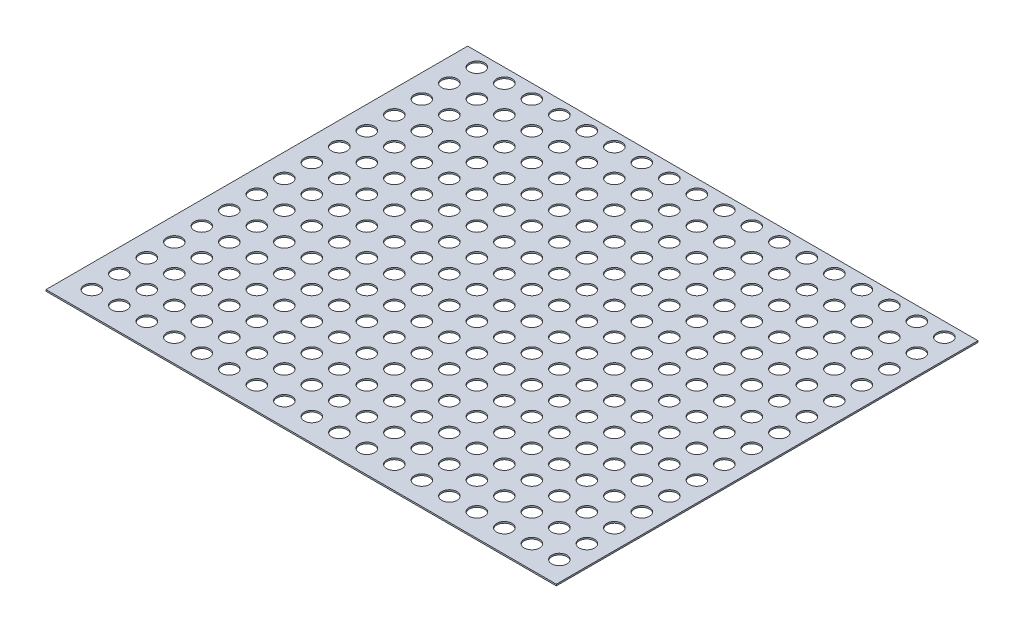
SolidWorks part; units mm, degrees
ref_plane "Спереди" through (0, 0, 0) normal (0, 0, 1) x (1, 0, 0)
ref_plane "Сверху" through (0, 0, 0) normal (0, 1, 0) x (1, 0, 0)
ref_plane "Справа" through (0, 0, 0) normal (1, 0, 0) x (0, 0, -1)
sketch "Эскиз1" plane through (0, 0, 0) normal (0, 1, 0) x (1, 0, 0)
  line L1 (167, -138) -> (-167, -138)
  line L2 (167, -138) -> (167, 138)
  line L3 (167, 138) -> (-167, 138)
  line L4 (-167, -138) -> (-167, 138)
  line L5 (167, -138) -> (-167, 138) construction
  line L6 (167, 138) -> (-167, -138) construction
  point P0 (0, 0)
  dimension "D1" = 334
  dimension "D2" = 276
extrude "Бобышка-Вытянуть1" add sketch "Эскиз1" along normal blind 1
sketch "Эскиз2" plane through (0, 1, 0) normal (0, 1, 0) x (1, 0, 0)
  line L0 (-167, 138) -> (-167, -138) construction
  line L2 (-167, -138) -> (167, -138) construction
  circle A0 centre (-152, -123) radius 5
  circle A1 centre (-134, -123) radius 5
  circle A2 centre (-116, -123) radius 5
  circle A3 centre (-98, -123) radius 5
  circle A4 centre (-80, -123) radius 5
  circle A5 centre (-62, -123) radius 5
  circle A6 centre (-44, -123) radius 5
  circle A7 centre (-26, -123) radius 5
  circle A8 centre (-8, -123) radius 5
  circle A9 centre (10, -123) radius 5
  circle A10 centre (28, -123) radius 5
  circle A11 centre (46, -123) radius 5
  circle A12 centre (64, -123) radius 5
  circle A13 centre (82, -123) radius 5
  circle A14 centre (100, -123) radius 5
  circle A15 centre (118, -123) radius 5
  circle A16 centre (136, -123) radius 5
  circle A17 centre (154, -123) radius 5
  circle A20 centre (-134, -105) radius 5
  circle A21 centre (-116, -105) radius 5
  circle A22 centre (-98, -105) radius 5
  circle A23 centre (-80, -105) radius 5
  circle A24 centre (-62, -105) radius 5
  circle A25 centre (-44, -105) radius 5
  circle A26 centre (-26, -105) radius 5
  circle A27 centre (-8, -105) radius 5
  circle A28 centre (10, -105) radius 5
  circle A29 centre (28, -105) radius 5
  circle A30 centre (46, -105) radius 5
  circle A31 centre (64, -105) radius 5
  circle A32 centre (82, -105) radius 5
  circle A33 centre (100, -105) radius 5
  circle A34 centre (118, -105) radius 5
  circle A35 centre (136, -105) radius 5
  circle A36 centre (154, -105) radius 5
  circle A39 centre (-134, -87) radius 5
  circle A40 centre (-116, -87) radius 5
  circle A41 centre (-98, -87) radius 5
  circle A42 centre (-80, -87) radius 5
  circle A43 centre (-62, -87) radius 5
  circle A44 centre (-44, -87) radius 5
  circle A45 centre (-26, -87) radius 5
  circle A46 centre (-8, -87) radius 5
  circle A47 centre (10, -87) radius 5
  circle A48 centre (28, -87) radius 5
  circle A49 centre (46, -87) radius 5
  circle A50 centre (64, -87) radius 5
  circle A51 centre (82, -87) radius 5
  circle A52 centre (100, -87) radius 5
  circle A53 centre (118, -87) radius 5
  circle A54 centre (136, -87) radius 5
  circle A55 centre (154, -87) radius 5
  circle A58 centre (-134, -69) radius 5
  circle A59 centre (-116, -69) radius 5
  circle A60 centre (-98, -69) radius 5
  circle A61 centre (-80, -69) radius 5
  circle A62 centre (-62, -69) radius 5
  circle A63 centre (-44, -69) radius 5
  circle A64 centre (-26, -69) radius 5
  circle A65 centre (-8, -69) radius 5
  circle A66 centre (10, -69) radius 5
  circle A67 centre (28, -69) radius 5
  circle A68 centre (46, -69) radius 5
  circle A69 centre (64, -69) radius 5
  circle A70 centre (82, -69) radius 5
  circle A71 centre (100, -69) radius 5
  circle A72 centre (118, -69) radius 5
  circle A73 centre (136, -69) radius 5
  circle A74 centre (154, -69) radius 5
  circle A77 centre (-134, -51) radius 5
  circle A78 centre (-116, -51) radius 5
  circle A79 centre (-98, -51) radius 5
  circle A80 centre (-80, -51) radius 5
  circle A81 centre (-62, -51) radius 5
  circle A82 centre (-44, -51) radius 5
  circle A83 centre (-26, -51) radius 5
  circle A84 centre (-8, -51) radius 5
  circle A85 centre (10, -51) radius 5
  circle A86 centre (28, -51) radius 5
  circle A87 centre (46, -51) radius 5
  circle A88 centre (64, -51) radius 5
  circle A89 centre (82, -51) radius 5
  circle A90 centre (100, -51) radius 5
  circle A91 centre (118, -51) radius 5
  circle A92 centre (136, -51) radius 5
  circle A93 centre (154, -51) radius 5
  circle A96 centre (-134, -33) radius 5
  circle A97 centre (-116, -33) radius 5
  circle A98 centre (-98, -33) radius 5
  circle A99 centre (-80, -33) radius 5
  circle A100 centre (-62, -33) radius 5
  circle A101 centre (-44, -33) radius 5
  circle A102 centre (-26, -33) radius 5
  circle A103 centre (-8, -33) radius 5
  circle A104 centre (10, -33) radius 5
  circle A105 centre (28, -33) radius 5
  circle A106 centre (46, -33) radius 5
  circle A107 centre (64, -33) radius 5
  circle A108 centre (82, -33) radius 5
  circle A109 centre (100, -33) radius 5
  circle A110 centre (118, -33) radius 5
  circle A111 centre (136, -33) radius 5
  circle A112 centre (154, -33) radius 5
  circle A115 centre (-134, -15) radius 5
  circle A116 centre (-116, -15) radius 5
  circle A117 centre (-98, -15) radius 5
  circle A118 centre (-80, -15) radius 5
  circle A119 centre (-62, -15) radius 5
  circle A120 centre (-44, -15) radius 5
  circle A121 centre (-26, -15) radius 5
  circle A122 centre (-8, -15) radius 5
  circle A123 centre (10, -15) radius 5
  circle A124 centre (28, -15) radius 5
  circle A125 centre (46, -15) radius 5
  circle A126 centre (64, -15) radius 5
  circle A127 centre (82, -15) radius 5
  circle A128 centre (100, -15) radius 5
  circle A129 centre (118, -15) radius 5
  circle A130 centre (136, -15) radius 5
  circle A131 centre (154, -15) radius 5
  circle A134 centre (-134, 3) radius 5
  circle A135 centre (-116, 3) radius 5
  circle A136 centre (-98, 3) radius 5
  circle A137 centre (-80, 3) radius 5
  circle A138 centre (-62, 3) radius 5
  circle A139 centre (-44, 3) radius 5
  circle A140 centre (-26, 3) radius 5
  circle A141 centre (-8, 3) radius 5
  circle A142 centre (10, 3) radius 5
  circle A143 centre (28, 3) radius 5
  circle A144 centre (46, 3) radius 5
  circle A145 centre (64, 3) radius 5
  circle A146 centre (82, 3) radius 5
  circle A147 centre (100, 3) radius 5
  circle A148 centre (118, 3) radius 5
  circle A149 centre (136, 3) radius 5
  circle A150 centre (154, 3) radius 5
  circle A153 centre (-134, 21) radius 5
  circle A154 centre (-116, 21) radius 5
  circle A155 centre (-98, 21) radius 5
  circle A156 centre (-80, 21) radius 5
  circle A157 centre (-62, 21) radius 5
  circle A158 centre (-44, 21) radius 5
  circle A159 centre (-26, 21) radius 5
  circle A160 centre (-8, 21) radius 5
  circle A161 centre (10, 21) radius 5
  circle A162 centre (28, 21) radius 5
  circle A163 centre (46, 21) radius 5
  circle A164 centre (64, 21) radius 5
  circle A165 centre (82, 21) radius 5
  circle A166 centre (100, 21) radius 5
  circle A167 centre (118, 21) radius 5
  circle A168 centre (136, 21) radius 5
  circle A169 centre (154, 21) radius 5
  circle A172 centre (-134, 39) radius 5
  circle A173 centre (-116, 39) radius 5
  circle A174 centre (-98, 39) radius 5
  circle A175 centre (-80, 39) radius 5
  circle A176 centre (-62, 39) radius 5
  circle A177 centre (-44, 39) radius 5
  circle A178 centre (-26, 39) radius 5
  circle A179 centre (-8, 39) radius 5
  circle A180 centre (10, 39) radius 5
  circle A181 centre (28, 39) radius 5
  circle A182 centre (46, 39) radius 5
  circle A183 centre (64, 39) radius 5
  circle A184 centre (82, 39) radius 5
  circle A185 centre (100, 39) radius 5
  circle A186 centre (118, 39) radius 5
  circle A187 centre (136, 39) radius 5
  circle A188 centre (154, 39) radius 5
  circle A191 centre (-134, 57) radius 5
  circle A192 centre (-116, 57) radius 5
  circle A193 centre (-98, 57) radius 5
  circle A194 centre (-80, 57) radius 5
  circle A195 centre (-62, 57) radius 5
  circle A196 centre (-44, 57) radius 5
  circle A197 centre (-26, 57) radius 5
  circle A198 centre (-8, 57) radius 5
  circle A199 centre (10, 57) radius 5
  circle A200 centre (28, 57) radius 5
  circle A201 centre (46, 57) radius 5
  circle A202 centre (64, 57) radius 5
  circle A203 centre (82, 57) radius 5
  circle A204 centre (100, 57) radius 5
  circle A205 centre (118, 57) radius 5
  circle A206 centre (136, 57) radius 5
  circle A207 centre (154, 57) radius 5
  circle A210 centre (-134, 75) radius 5
  circle A211 centre (-116, 75) radius 5
  circle A212 centre (-98, 75) radius 5
  circle A213 centre (-80, 75) radius 5
  circle A214 centre (-62, 75) radius 5
  circle A215 centre (-44, 75) radius 5
  circle A216 centre (-26, 75) radius 5
  circle A217 centre (-8, 75) radius 5
  circle A218 centre (10, 75) radius 5
  circle A219 centre (28, 75) radius 5
  circle A220 centre (46, 75) radius 5
  circle A221 centre (64, 75) radius 5
  circle A222 centre (82, 75) radius 5
  circle A223 centre (100, 75) radius 5
  circle A224 centre (118, 75) radius 5
  circle A225 centre (136, 75) radius 5
  circle A226 centre (154, 75) radius 5
  circle A229 centre (-134, 93) radius 5
  circle A230 centre (-116, 93) radius 5
  circle A231 centre (-98, 93) radius 5
  circle A232 centre (-80, 93) radius 5
  circle A233 centre (-62, 93) radius 5
  circle A234 centre (-44, 93) radius 5
  circle A235 centre (-26, 93) radius 5
  circle A236 centre (-8, 93) radius 5
  circle A237 centre (10, 93) radius 5
  circle A238 centre (28, 93) radius 5
  circle A239 centre (46, 93) radius 5
  circle A240 centre (64, 93) radius 5
  circle A241 centre (82, 93) radius 5
  circle A242 centre (100, 93) radius 5
  circle A243 centre (118, 93) radius 5
  circle A244 centre (136, 93) radius 5
  circle A245 centre (154, 93) radius 5
  circle A248 centre (-134, 111) radius 5
  circle A249 centre (-116, 111) radius 5
  circle A250 centre (-98, 111) radius 5
  circle A251 centre (-80, 111) radius 5
  circle A252 centre (-62, 111) radius 5
  circle A253 centre (-44, 111) radius 5
  circle A254 centre (-26, 111) radius 5
  circle A255 centre (-8, 111) radius 5
  circle A256 centre (10, 111) radius 5
  circle A257 centre (28, 111) radius 5
  circle A258 centre (46, 111) radius 5
  circle A259 centre (64, 111) radius 5
  circle A260 centre (82, 111) radius 5
  circle A261 centre (100, 111) radius 5
  circle A262 centre (118, 111) radius 5
  circle A263 centre (136, 111) radius 5
  circle A264 centre (154, 111) radius 5
  circle A267 centre (-134, 129) radius 5
  circle A268 centre (-116, 129) radius 5
  circle A269 centre (-98, 129) radius 5
  circle A270 centre (-80, 129) radius 5
  circle A271 centre (-62, 129) radius 5
  circle A272 centre (-44, 129) radius 5
  circle A273 centre (-26, 129) radius 5
  circle A274 centre (-8, 129) radius 5
  circle A275 centre (10, 129) radius 5
  circle A276 centre (28, 129) radius 5
  circle A277 centre (46, 129) radius 5
  circle A278 centre (64, 129) radius 5
  circle A279 centre (82, 129) radius 5
  circle A280 centre (100, 129) radius 5
  circle A281 centre (118, 129) radius 5
  circle A282 centre (136, 129) radius 5
  circle A283 centre (154, 129) radius 5
  circle A286 centre (-152, -105) radius 5
  circle A287 centre (-152, -87) radius 5
  circle A288 centre (-152, -69) radius 5
  circle A289 centre (-152, -51) radius 5
  circle A290 centre (-152, -33) radius 5
  circle A291 centre (-152, -15) radius 5
  circle A292 centre (-152, 3) radius 5
  circle A293 centre (-152, 21) radius 5
  circle A294 centre (-152, 39) radius 5
  circle A295 centre (-152, 57) radius 5
  circle A296 centre (-152, 75) radius 5
  circle A297 centre (-152, 93) radius 5
  circle A298 centre (-152, 111) radius 5
  circle A299 centre (-152, 129) radius 5
  dimension "D1" = 10
  dimension "D2" = 15
  dimension "D3" = 15
  dimension "D4" = 18
  dimension "D5" = 15
extrude "Вырез-Вытянуть1" cut sketch "Эскиз2" against normal through all both and the other way through all
